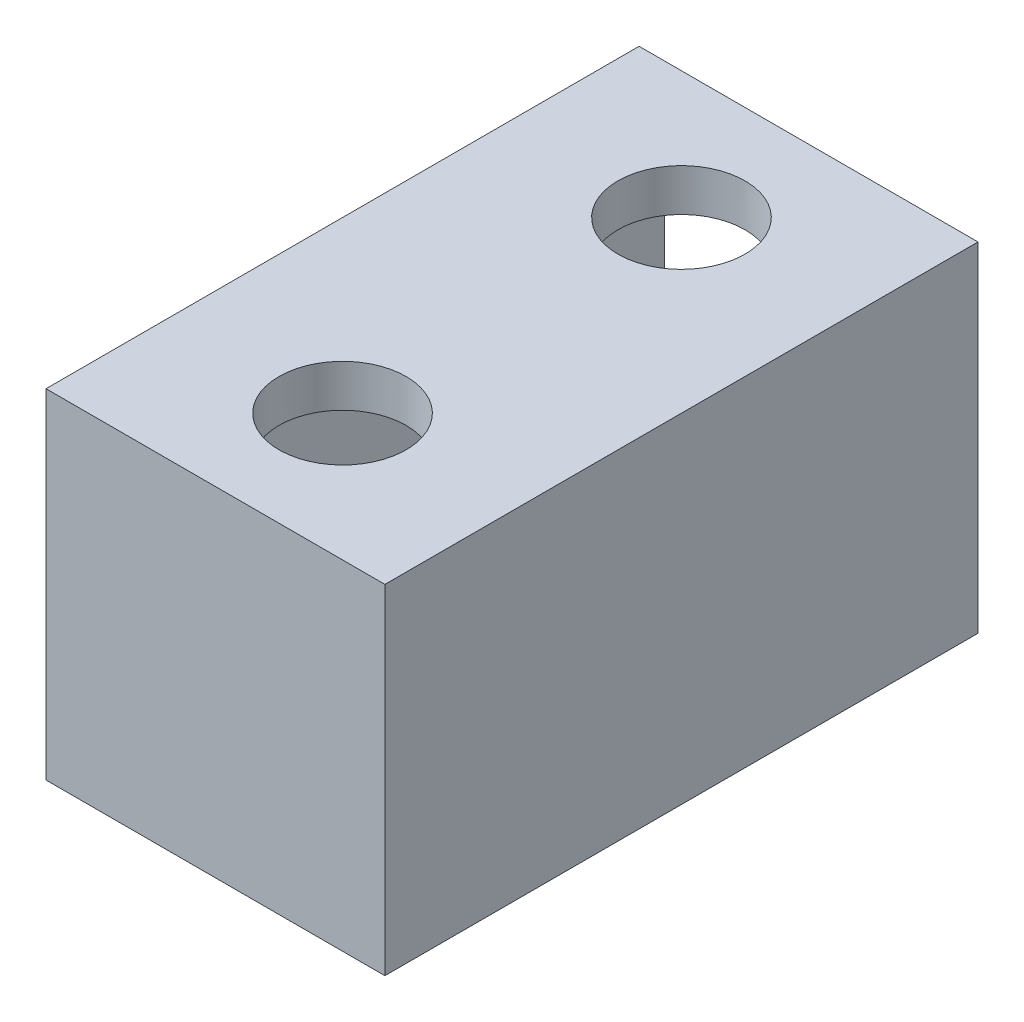
SolidWorks part; units mm, degrees
ref_plane "Front Plane" through (0, 0, 0) normal (0, 0, 1) x (1, 0, 0)
ref_plane "Top Plane" through (0, 0, 0) normal (0, 1, 0) x (1, 0, 0)
ref_plane "Right Plane" through (0, 0, 0) normal (1, 0, 0) x (0, 0, -1)
sketch "Sketch1" plane through (0, 0, 0) normal (0, 0, 1) x (1, 0, 0)
  line L1 (0, 0) -> (-40, 0)
  line L2 (0, 0) -> (0, 40)
  line L3 (0, 40) -> (-40, 40)
  line L4 (-40, 0) -> (-40, 40)
  line L5 (-37, 37) -> (-3, 37)
  line L6 (-37, 37) -> (-37, 3)
  line L7 (-37, 3) -> (-3, 3)
  line L8 (-3, 37) -> (-3, 3)
  dimension "D1" = 40
  dimension "D2" = 40
  dimension "D3" = 3
  dimension "D4" = 3
  dimension "D5" = 3
  dimension "D6" = 3
extrude "Boss-Extrude1" add sketch "Sketch1" along normal blind 70
sketch "Sketch2" plane through (0, 37, 0) normal (0, -1, 0) x (-1, 0, 0)
  line L0 (37, -70) -> (37, 0) construction
  line L1 (3, -70) -> (37, -70)
  line L2 (3, -70) -> (3, -67)
  line L3 (3, -67) -> (37, -67)
  line L4 (37, -70) -> (37, -67)
  dimension "D1" = 3
extrude "Boss-Extrude2" add sketch "Sketch2" along normal blind 37
sketch "Sketch3" plane through (0, 40, 0) normal (0, 1, 0) x (1, 0, 0)
  line L0 (-20, 0) -> (-20, -70)
  line L1 (0, 0) -> (-40, 0) construction
  line L2 (0, -70) -> (-40, -70) construction
  line L4 (-9.4505, -15) -> (-30.5495, -15)
  line L5 (-9.4505, -15) -> (-9.4505, -55)
  line L6 (-9.4505, -55) -> (-30.5495, -55)
  line L7 (-30.5495, -15) -> (-30.5495, -55)
  line L8 (-9.4505, -15) -> (-30.5495, -55) construction
  line L9 (-9.4505, -55) -> (-30.5495, -15) construction
  circle A0 centre (-20, -15) radius 7.5
  circle A1 centre (-20, -55) radius 7.5
  point P6 (-20, -35)
  dimension "D2" = 15
  dimension "D3" = 15
  dimension "D1" = 40
extrude "Cut-Extrude1" cut sketch "Sketch3" against normal blind 37 contours L0 A0 L4 | L4 A0 L0 | L0 A0 L4 | L4 A0 L0 | L0 A1 L6 | L6 A1 L0 | L0 A1 L6 | L6 A1 L0
sketch "Sketch4" plane through (0, 37, 0) normal (0, -1, 0) x (-1, 0, 0)
  circle A0 centre (20, -15) radius 8.5
  circle A1 centre (20, -55) radius 8.5
  circle A2 centre (20, -15) radius 7.5
  circle A3 centre (20, -55) radius 7.5
  dimension "D1" = 17
  dimension "D2" = 17
extrude "Boss-Extrude3" add sketch "Sketch4" along normal blind 2
sketch "Sketch6" plane through (0, 3, 0) normal (0, 1, 0) x (1, 0, 0)
  circle A0 centre (-20, -15) radius 7.5
  circle A1 centre (-20, -55) radius 7.5
extrude "Boss-Extrude4" add sketch "Sketch6" against normal blind 10
fillet "Fillet2" radius 1.5 1 edges at (-20, -7, 62.5)
fillet "Fillet3" radius 1.5 1 edges at (-20, -7, 22.5)
fillet "Fillet4" radius 1.5 1 edges at (-27.5, 0, 15)
fillet "Fillet5" radius 1.5 1 edges at (-27.5, 0, 55)
sketch "Sketch9" plane through (-40, 0, 0) normal (-1, 0, 0) x (0, 0, 1)
  line L0 (0, 20) -> (70, 20)
  line L1 (0, 40) -> (0, 0) construction
  line L2 (70, 40) -> (70, 0) construction
  line L3 (35, 40) -> (35, 0)
  line L4 (70, 40) -> (0, 40) construction
  line L5 (70, 0) -> (0, 0) construction
  line L6 (35, 30.4882) -> (37.4654, 28.0228)
  line L7 (37.4654, 28.0228) -> (36.2327, 28.0228)
  line L8 (36.2327, 28.0228) -> (36.2327, 12.2657)
  line L9 (36.2327, 12.2657) -> (33.4123, 12.2657)
  line L10 (33.4123, 12.2657) -> (33.4123, 28.0228)
  line L11 (32.5346, 28.0228) -> (35, 30.4882)
  line L12 (33.4123, 28.0228) -> (32.5346, 28.0228)
extrude "Boss-Extrude5" add sketch "Sketch9" along normal blind 2 contours L12 L11 L6 L7 L8 L9 L10
